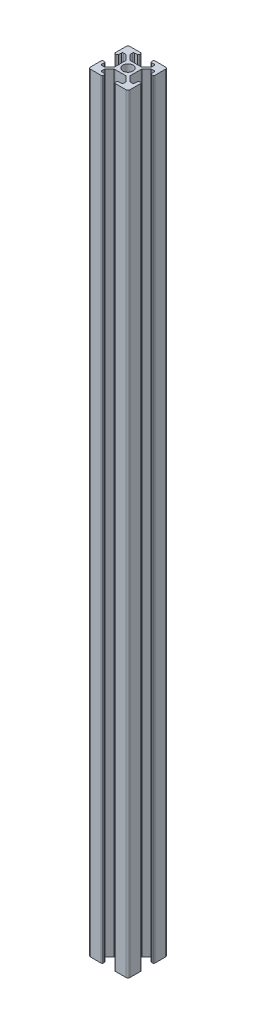
SolidWorks part; units mm, degrees
ref_plane "Front Plane" through (0, 0, 0) normal (0, 0, 1) x (1, 0, 0)
ref_plane "Top Plane" through (0, 0, 0) normal (0, 1, 0) x (1, 0, 0)
ref_plane "Right Plane" through (0, 0, 0) normal (1, 0, 0) x (0, 0, -1)
ref_plane "Plane1" through (0, 195, 0) normal (0, 1, 0) x (1, 0, 0)
sketch "Sketch1" plane through (0, 195, 0) normal (0, 1, 0) x (1, 0, 0)
  line L0 (-3.1, 8.85) -> (-3.1, 9.5)
  line L1 (-3.6, 10) -> (-9, 10)
  line L2 (-10, 9) -> (-10, 3.6)
  line L3 (-9.5, 3.1) -> (-8.85, 3.1)
  line L4 (-8.35, 3.6) -> (-8.35, 5)
  line L5 (-7.85, 5.5) -> (-6.6263, 5.5)
  line L6 (-6.2728, 5.3536) -> (-4.0464, 3.1272)
  line L7 (-3.9, 2.7737) -> (-3.9, -2.7737)
  line L8 (-4.0464, -3.1272) -> (-6.2728, -5.3536)
  line L9 (-6.6263, -5.5) -> (-7.85, -5.5)
  line L10 (-8.35, -5) -> (-8.35, -3.6)
  line L11 (-8.85, -3.1) -> (-9.5, -3.1)
  line L12 (-10, -3.6) -> (-10, -9)
  line L13 (-9, -10) -> (-3.6, -10)
  line L14 (-3.1, -9.5) -> (-3.1, -8.85)
  line L15 (-3.6, -8.35) -> (-5, -8.35)
  line L16 (-5.5, -7.85) -> (-5.5, -6.6263)
  line L17 (-5.3536, -6.2728) -> (-3.1272, -4.0464)
  line L18 (-2.7737, -3.9) -> (2.7737, -3.9)
  line L19 (3.1272, -4.0464) -> (5.3536, -6.2728)
  line L20 (5.5, -6.6263) -> (5.5, -7.85)
  line L21 (5, -8.35) -> (3.6, -8.35)
  line L22 (3.1, -8.85) -> (3.1, -9.5)
  line L23 (3.6, -10) -> (9, -10)
  line L24 (10, -9) -> (10, -3.6)
  line L25 (9.5, -3.1) -> (8.85, -3.1)
  line L26 (8.35, -3.6) -> (8.35, -5)
  line L27 (7.85, -5.5) -> (6.6263, -5.5)
  line L28 (6.2728, -5.3536) -> (4.0464, -3.1272)
  line L29 (3.9, -2.7737) -> (3.9, 2.7737)
  line L30 (4.0464, 3.1272) -> (6.2728, 5.3536)
  line L31 (6.6263, 5.5) -> (7.85, 5.5)
  line L32 (8.35, 5) -> (8.35, 3.6)
  line L33 (8.85, 3.1) -> (9.5, 3.1)
  line L34 (10, 3.6) -> (10, 9)
  line L35 (9, 10) -> (3.6, 10)
  line L36 (3.1, 9.5) -> (3.1, 8.85)
  line L37 (3.6, 8.35) -> (5, 8.35)
  line L38 (5.5, 7.85) -> (5.5, 6.6263)
  line L39 (5.3536, 6.2728) -> (3.1272, 4.0464)
  line L40 (2.7737, 3.9) -> (-2.7737, 3.9)
  line L41 (-3.1272, 4.0464) -> (-5.5, 6.4192)
  line L42 (-5.5, 6.4192) -> (-5.5, 7.85)
  line L43 (-5, 8.35) -> (-3.6, 8.35)
  circle A0 centre (0, 0) radius 2.6
  arc A1 (-3.1, 9.5) -> (-3.6, 10) centre (-3.6, 9.5) ccw
  arc A2 (-9, 10) -> (-10, 9) centre (-9, 9) ccw
  arc A3 (-10, 3.6) -> (-9.5, 3.1) centre (-9.5, 3.6) ccw
  arc A4 (-8.85, 3.1) -> (-8.35, 3.6) centre (-8.85, 3.6) ccw
  arc A5 (-8.35, 5) -> (-7.85, 5.5) centre (-7.85, 5) cw
  arc A6 (-6.6263, 5.5) -> (-6.2728, 5.3536) centre (-6.6263, 5) cw
  arc A7 (-4.0464, 3.1272) -> (-3.9, 2.7737) centre (-4.4, 2.7737) cw
  arc A8 (-3.9, -2.7737) -> (-4.0464, -3.1272) centre (-4.4, -2.7737) cw
  arc A9 (-6.2728, -5.3536) -> (-6.6263, -5.5) centre (-6.6263, -5) cw
  arc A10 (-7.85, -5.5) -> (-8.35, -5) centre (-7.85, -5) cw
  arc A11 (-8.35, -3.6) -> (-8.85, -3.1) centre (-8.85, -3.6) ccw
  arc A12 (-9.5, -3.1) -> (-10, -3.6) centre (-9.5, -3.6) ccw
  arc A13 (-10, -9) -> (-9, -10) centre (-9, -9) ccw
  arc A14 (-3.6, -10) -> (-3.1, -9.5) centre (-3.6, -9.5) ccw
  arc A15 (-3.1, -8.85) -> (-3.6, -8.35) centre (-3.6, -8.85) ccw
  arc A16 (-5, -8.35) -> (-5.5, -7.85) centre (-5, -7.85) cw
  arc A17 (-5.5, -6.6263) -> (-5.3536, -6.2728) centre (-5, -6.6263) cw
  arc A18 (-3.1272, -4.0464) -> (-2.7737, -3.9) centre (-2.7737, -4.4) cw
  arc A19 (2.7737, -3.9) -> (3.1272, -4.0464) centre (2.7737, -4.4) cw
  arc A20 (5.3536, -6.2728) -> (5.5, -6.6263) centre (5, -6.6263) cw
  arc A21 (5.5, -7.85) -> (5, -8.35) centre (5, -7.85) cw
  arc A22 (3.6, -8.35) -> (3.1, -8.85) centre (3.6, -8.85) ccw
  arc A23 (3.1, -9.5) -> (3.6, -10) centre (3.6, -9.5) ccw
  arc A24 (9, -10) -> (10, -9) centre (9, -9) ccw
  arc A25 (10, -3.6) -> (9.5, -3.1) centre (9.5, -3.6) ccw
  arc A26 (8.85, -3.1) -> (8.35, -3.6) centre (8.85, -3.6) ccw
  arc A27 (8.35, -5) -> (7.85, -5.5) centre (7.85, -5) cw
  arc A28 (6.6263, -5.5) -> (6.2728, -5.3536) centre (6.6263, -5) cw
  arc A29 (4.0464, -3.1272) -> (3.9, -2.7737) centre (4.4, -2.7737) cw
  arc A30 (3.9, 2.7737) -> (4.0464, 3.1272) centre (4.4, 2.7737) cw
  arc A31 (6.2728, 5.3536) -> (6.6263, 5.5) centre (6.6263, 5) cw
  arc A32 (7.85, 5.5) -> (8.35, 5) centre (7.85, 5) cw
  arc A33 (8.35, 3.6) -> (8.85, 3.1) centre (8.85, 3.6) ccw
  arc A34 (9.5, 3.1) -> (10, 3.6) centre (9.5, 3.6) ccw
  arc A35 (10, 9) -> (9, 10) centre (9, 9) ccw
  arc A36 (3.6, 10) -> (3.1, 9.5) centre (3.6, 9.5) ccw
  arc A37 (3.1, 8.85) -> (3.6, 8.35) centre (3.6, 8.85) ccw
  arc A38 (5, 8.35) -> (5.5, 7.85) centre (5, 7.85) cw
  arc A39 (5.5, 6.6263) -> (5.3536, 6.2728) centre (5, 6.6263) cw
  arc A40 (3.1272, 4.0464) -> (2.7737, 3.9) centre (2.7737, 4.4) cw
  arc A41 (-2.7737, 3.9) -> (-3.1272, 4.0464) centre (-2.7737, 4.4) cw
  arc A42 (-5.5, 7.85) -> (-5, 8.35) centre (-5, 7.85) cw
  arc A43 (-3.6, 8.35) -> (-3.1, 8.85) centre (-3.6, 8.85) ccw
extrude "Boss-Extrude1" add sketch "Sketch1" against normal blind 390
